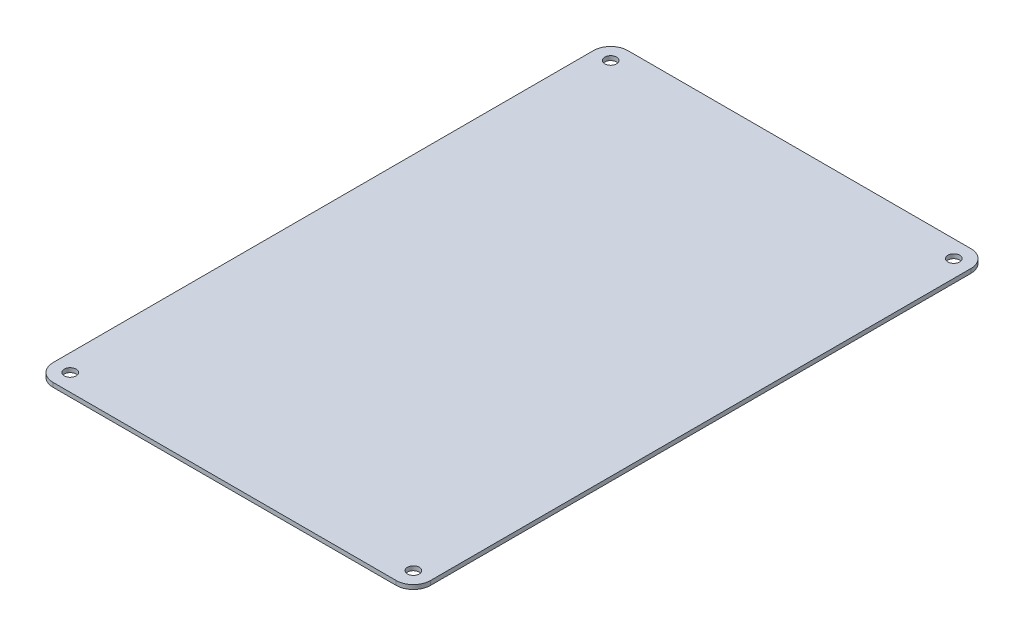
SolidWorks part; units mm, degrees
ref_plane "Front Plane" through (0, 0, 0) normal (0, 0, 1) x (1, 0, 0)
ref_plane "Top Plane" through (0, 0, 0) normal (0, 1, 0) x (1, 0, 0)
ref_plane "Right Plane" through (0, 0, 0) normal (1, 0, 0) x (0, 0, -1)
sketch "Sketch1" plane through (0, 0, 0) normal (0, 1, 0) x (1, 0, 0)
  line L1 (6.35, 0) -> (133.35, 0)
  line L2 (0, 6.35) -> (0, 206.375)
  line L3 (6.35, 212.725) -> (133.35, 212.725)
  line L4 (139.7, 6.35) -> (139.7, 206.375)
  circle A0 centre (6.35, 206.375) radius 2.1828
  circle A1 centre (133.35, 206.375) radius 2.1828
  circle A2 centre (6.35, 6.35) radius 2.1828
  circle A3 centre (133.35, 6.35) radius 2.1828
  arc A4 (6.35, 0) -> (0, 6.35) centre (6.35, 6.35) cw
  arc A5 (133.35, 0) -> (139.7, 6.35) centre (133.35, 6.35) ccw
  arc A6 (139.7, 206.375) -> (133.35, 212.725) centre (133.35, 206.375) ccw
  arc A7 (6.35, 212.725) -> (0, 206.375) centre (6.35, 206.375) ccw
  point P15 (0, 0)
  point P18 (139.7, 0)
  point P23 (0, 212.725)
  dimension "D5" = 4.3656
  dimension "D8" = 4.3656
  dimension "D11" = 4.3656
  dimension "D14" = 4.3656
  dimension "D15" = 6.35
  dimension "D1" = 139.7
  dimension "D2" = 212.725
  dimension "D3" = 6.35
  dimension "D4" = 6.35
  dimension "D6" = 6.35
  dimension "D7" = 6.35
  dimension "D9" = 6.35
  dimension "D10" = 6.35
  dimension "D12" = 6.35
  dimension "D13" = 6.35
extrude "Boss-Extrude1" add sketch "Sketch1" along normal mid plane 1.5875
